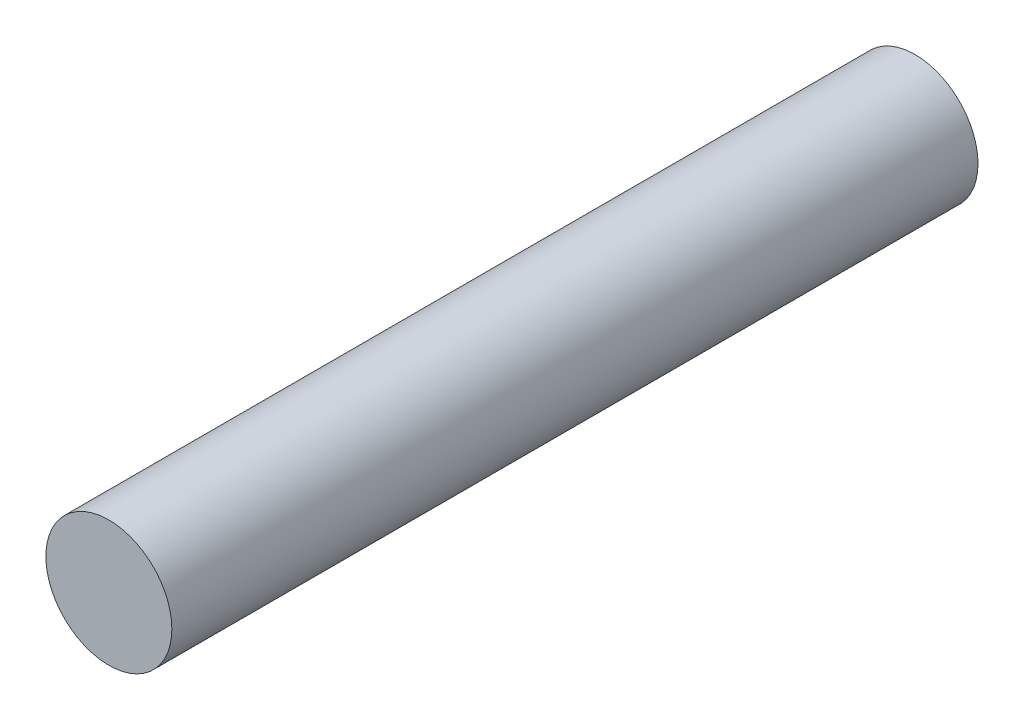
SolidWorks part; units mm, degrees
ref_plane "Front" through (0, 0, 0) normal (0, 0, 1) x (1, 0, 0)
ref_plane "Top" through (0, 0, 0) normal (0, 1, 0) x (1, 0, 0)
ref_plane "Right" through (0, 0, 0) normal (1, 0, 0) x (0, 0, -1)
sketch "Sketch1" plane through (0, 0, 0) normal (0, 0, 1) x (1, 0, 0)
  circle A0 centre (0, 0) radius 1.9844
  dimension "D1" = 3.9688
extrude "Boss-Extrude1" add sketch "Sketch1" along normal blind 25.4
